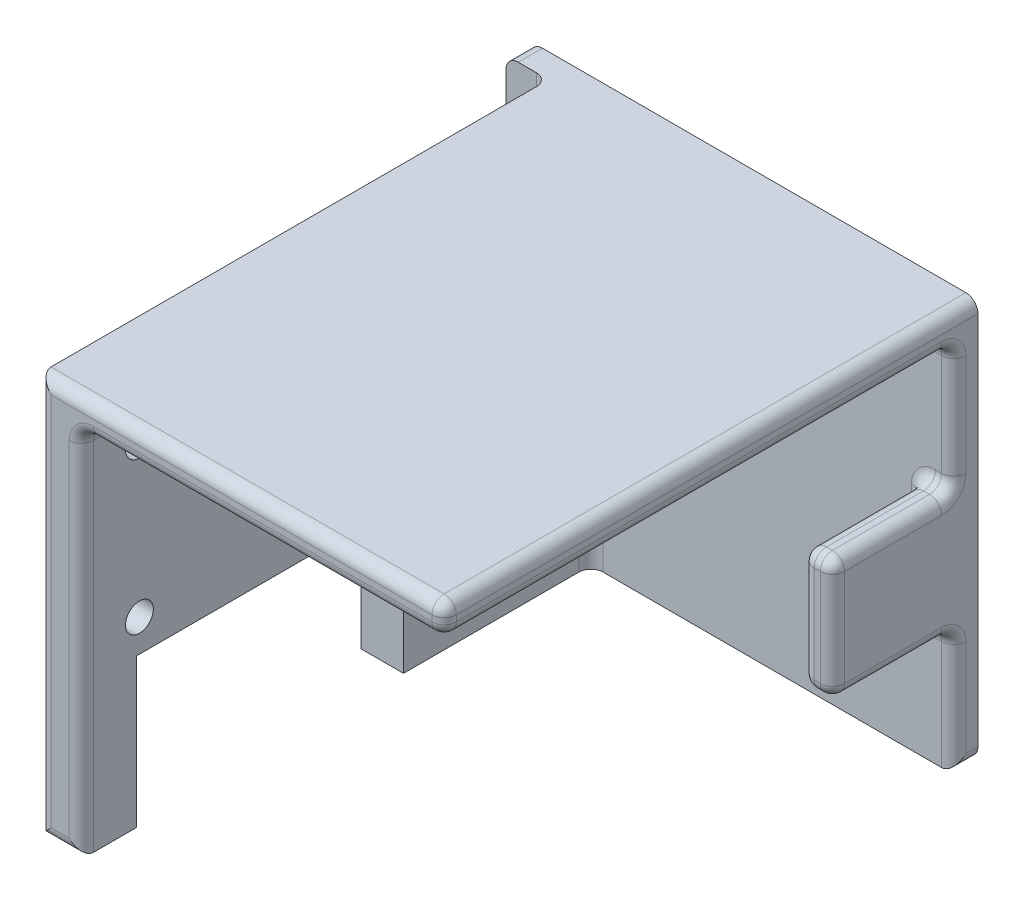
SolidWorks part; units mm, degrees
ref_plane "Front Plane" through (0, 0, 0) normal (0, 0, 1) x (1, 0, 0)
ref_plane "Top Plane" through (0, 0, 0) normal (0, 1, 0) x (1, 0, 0)
ref_plane "Right Plane" through (0, 0, 0) normal (1, 0, 0) x (0, 0, -1)
sketch "Sketch1" plane through (0, 0, 0) normal (0, 0, 1) x (1, 0, 0)
  line L4 (0, 32.9) -> (36.9, 32.9)
  line L5 (0, 32.9) -> (0, 0)
  line L6 (0, 0) -> (36.9, 0)
  line L7 (36.9, 32.9) -> (36.9, 0)
  line L8 (0, 32.9) -> (36.9, 0) construction
  line L9 (0, 0) -> (36.9, 32.9) construction
  circle A0 centre (18.45, 16.45) radius 1.5
  point P0 (18.45, 16.45)
  dimension "D2" = 3
  dimension "D1" = 32.9
  dimension "D3" = 36.9
extrude "Boss-Extrude1" add sketch "Sketch1" along normal blind 2
sketch "Sketch2" plane through (0, 0, 2) normal (0, 0, 1) x (1, 0, 0)
  line L0 (3.5, 0) -> (7, 0)
  line L2 (7, 0) -> (7, 30.4)
  line L3 (7, 30.4) -> (36.9, 30.4)
  line L4 (36.9, 0) -> (36.9, 32.9) construction
  line L5 (36.9, 30.4) -> (36.9, 32.9)
  line L6 (36.9, 32.9) -> (3.5, 32.9)
  line L7 (3.5, 32.9) -> (3.5, 0)
  line L9 (0, 0) -> (36.9, 0) construction
  line L10 (0, 32.9) -> (0, 0) construction
  dimension "D1" = 3.5
  dimension "D2" = 2.5
  dimension "D3" = 3.5
extrude "Boss-Extrude2" add sketch "Sketch2" along normal blind 42
sketch "Sketch5" plane through (0, 0, 2) normal (0, 0, 1) x (1, 0, 0)
  line L0 (36.9, 20) -> (34.4, 20)
  line L1 (36.9, 0) -> (36.9, 30.4) construction
  line L2 (34.4, 20) -> (34.4, 10)
  line L3 (34.4, 10) -> (36.9, 10)
  line L4 (36.9, 10) -> (36.9, 20)
  line L6 (7, 0) -> (36.9, 0) construction
  dimension "D1" = 2.5
  dimension "D2" = 10
  dimension "D3" = 10
extrude "Boss-Extrude3" add sketch "Sketch5" along normal blind 10
fillet "Fillet1" radius 1 28 edges at (7, 15.2, 44) (0, 32.9, 1) (36.9, 0, 1) (0, 0, 1) (5.25, 0, 44) (3.5, 16.45, 44) (20.2, 32.9, 44) (21.95, 30.4, 44) (36.9, 31.65, 44) (36.9, 32.9, 22) (7, 30.4, 23) (21.95, 30.4, 2) (7, 15.2, 2) (36.9, 15, 12) (34.4, 15, 12) (34.4, 10, 7) (34.4, 20, 7) (36.9, 20, 7) (36.9, 10, 7) (35.65, 10, 12) (35.65, 20, 12) (36.9, 30.4, 23) (36.9, 25.2, 2) (36.9, 5, 2) (35.65, 20, 2) (35.65, 10, 2) (34.4, 15, 2) (3.5, 16.45, 2)
sketch "Sketch3" plane through (7, 0, 0) normal (1, 0, 0) x (0, 0, -1)
  line L0 (-41.015, 29.4) -> (-15.885, 5.25) construction
  line L1 (-15.885, 5.25) -> (-15.885, 29.4) construction
  line L5 (-15.885, 29.4) -> (-41.015, 29.4) construction
  line L6 (-28.45, 17.325) -> (-28.45, 15.2) construction
  line L7 (-32.7, 19.45) -> (-24.2, 10.95) construction
  line L8 (-24.2, 19.45) -> (-32.7, 10.95) construction
  line L9 (-41.015, 29.4) -> (-41.015, 5.25) construction
  line L10 (-41.015, 5.25) -> (-15.885, 5.25) construction
  line L11 (-15.885, 29.4) -> (-41.015, 5.25) construction
  line L12 (-2, 29.4) -> (-2, 0) construction
  line L13 (-32.7, 19.45) -> (-32.7, 10.95) construction
  line L14 (-32.7, 10.95) -> (-24.2, 10.95) construction
  line L15 (-24.2, 10.95) -> (-24.2, 19.45) construction
  line L16 (-24.2, 19.45) -> (-32.7, 19.45) construction
  line L17 (-30.2917, 15.2) -> (-26.6083, 15.2) construction
  line L18 (-34.6369, 17.325) -> (-22.2631, 17.325) construction
  line L21 (-43, 30.4) -> (-3, 30.4) construction
  line L22 (-43, 0) -> (-3, 0) construction
  line L23 (-39.45, 12.25) -> (-17.45, 12.25)
  line L24 (-17.45, 12.25) -> (-17.45, 0)
  line L25 (-17.45, 0) -> (-39.45, 0)
  line L26 (-39.45, 0) -> (-39.45, 12.25)
  circle A4 centre (-39.215, 27.4) radius 1.15
  circle A5 centre (-17.685, 27.4) radius 1.15
  circle A6 centre (-39.215, 14.9) radius 1.15
  circle A7 centre (-17.685, 14.9) radius 1.15
  point P6 (-28.45, 17.325)
  point P19 (-28.45, 17.325)
  point P20 (-28.45, 15.2)
  point P23 (-28.45, 15.2)
  point P27 (-28.45, 19.45)
  dimension "D1" = 25.13
  dimension "D7" = 2.3
  dimension "D2" = 24.15
  dimension "D3" = 26.45
  dimension "D4" = 8.5
  dimension "D5" = 8.5
  dimension "D6" = 14.2
  dimension "D8" = 12.5
  dimension "D9" = 1.8
  dimension "D10" = 1.8
  dimension "D11" = 2
  dimension "D12" = 7
  dimension "D13" = 22
extrude "Cut-Extrude1" cut sketch "Sketch3" against normal up to next
